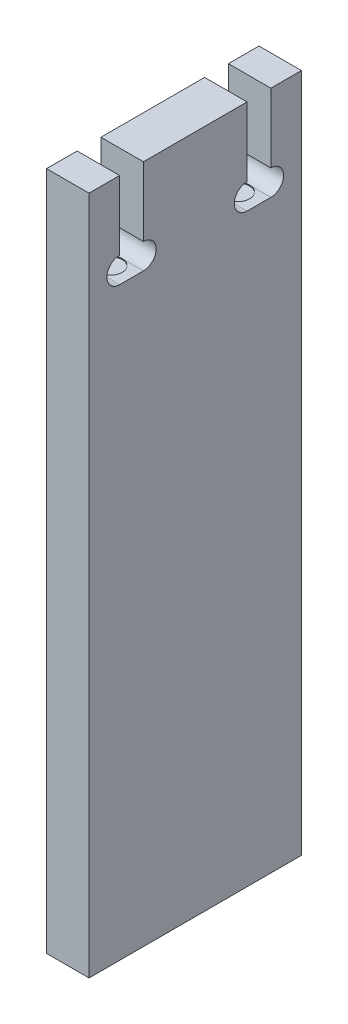
SolidWorks part; units mm, degrees
ref_plane "前视基准面" through (0, 0, 0) normal (0, 0, 1) x (1, 0, 0)
ref_plane "上视基准面" through (0, 0, 0) normal (0, 1, 0) x (1, 0, 0)
ref_plane "右视基准面" through (0, 0, 0) normal (1, 0, 0) x (0, 0, -1)
sketch "草图1" plane through (0, 0, 0) normal (1, 0, 0) x (0, 0, -1)
  line L0 (6.4, 80) -> (18.6, 80)
  line L1 (21.4, 80) -> (25, 80)
  line L7 (0, 80) -> (0, 0)
  line L8 (0, 0) -> (25, 0)
  line L9 (21.4, 80) -> (21.4, 71.8744)
  line L10 (18.6, 71.8744) -> (18.6, 80)
  line L11 (18.6, 68.8744) -> (21.4, 68.8744)
  line L12 (3.6, 80) -> (3.6, 71.8744)
  line L13 (6.4, 71.8744) -> (6.4, 80)
  line L14 (6.4, 68.8744) -> (3.6, 68.8744)
  line L15 (0, 80) -> (3.6, 80)
  line L16 (25, 80) -> (25, 0)
  circle A4 centre (4.5, 5) radius 1.4
  circle A5 centre (20.5, 5) radius 1.4
  arc A6 (18.6, 71.8744) -> (18.6, 68.8744) centre (18.6, 70.3744) ccw
  arc A7 (21.4, 68.8744) -> (21.4, 71.8744) centre (21.4, 70.3744) ccw
  arc A8 (6.4, 68.8744) -> (6.4, 71.8744) centre (6.4, 70.3744) ccw
  arc A9 (3.6, 71.8744) -> (3.6, 68.8744) centre (3.6, 70.3744) ccw
extrude "凸台-拉伸1" add sketch "草图1" along normal mid plane 5 contours L7 L8 L16 L1 L9 A7 L11 A6 L10 L0 L13 A8 L14 A9 L12 L15
sketch "草图2" plane through (0, 68.8744, 0) normal (0, 1, 0) x (1, 0, 0)
  circle A0 centre (0, 20) radius 1.4
  circle A1 centre (0, 5) radius 1.4
extrude "切除-拉伸1" cut sketch "草图2" against normal blind 0.1
